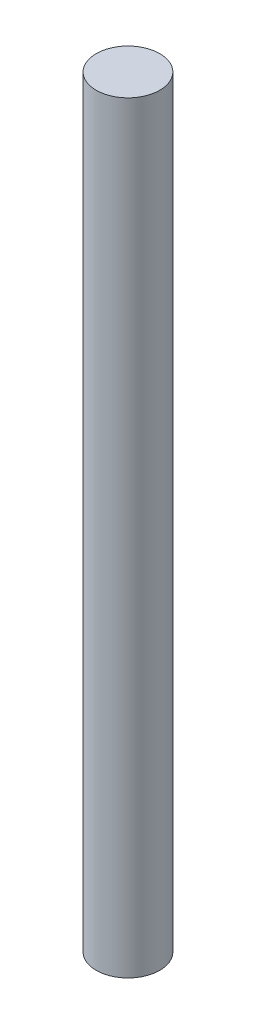
SolidWorks part; units mm, degrees
ref_plane "Front Plane" through (0, 0, 0) normal (0, 0, 1) x (1, 0, 0)
ref_plane "Top Plane" through (0, 0, 0) normal (0, 1, 0) x (1, 0, 0)
ref_plane "Right Plane" through (0, 0, 0) normal (1, 0, 0) x (0, 0, -1)
sketch "Sketch1" plane through (0, 0, 0) normal (0, 1, 0) x (1, 0, 0)
  circle A0 centre (0, 0) radius 0.3969
  dimension "D1" = 0.7937
extrude "Boss-Extrude1" add sketch "Sketch1" along normal blind 9.525
